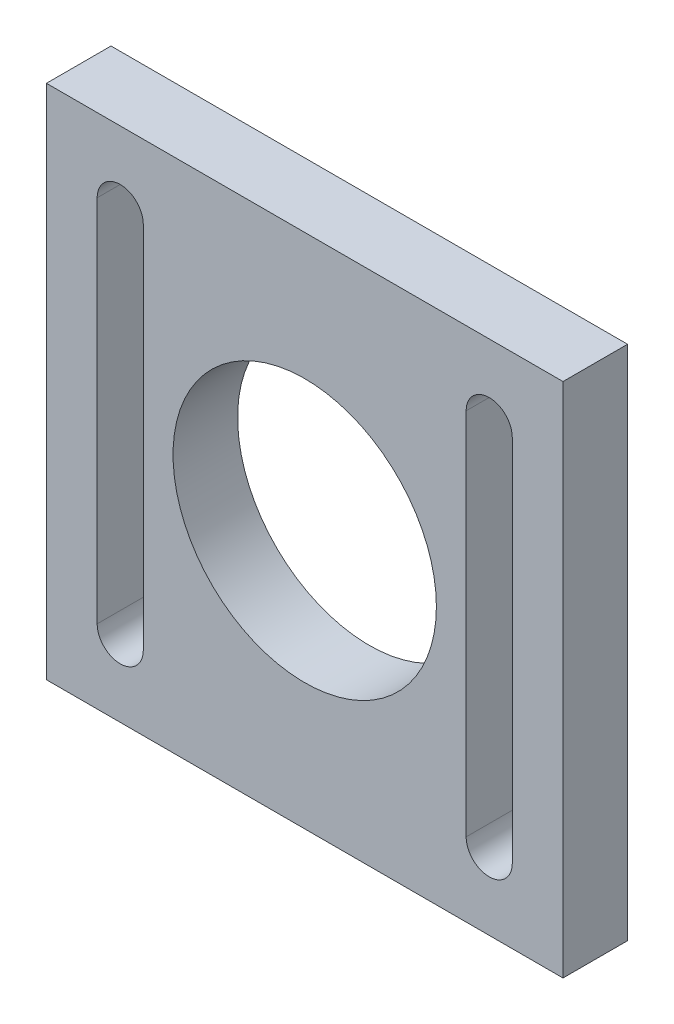
SolidWorks part; units mm, degrees
ref_plane "Front Plane" through (0, 0, 0) normal (0, 0, 1) x (1, 0, 0)
ref_plane "Top Plane" through (0, 0, 0) normal (0, 1, 0) x (1, 0, 0)
ref_plane "Right Plane" through (0, 0, 0) normal (1, 0, 0) x (0, 0, -1)
sketch "Sketch1" plane through (0, 0, 0) normal (0, 0, 1) x (1, 0, 0)
  line L1 (0, 0) -> (56, 0)
  line L2 (0, 0) -> (0, 56)
  line L3 (0, 56) -> (56, 56)
  line L4 (56, 0) -> (56, 56)
  dimension "D1" = 56
  dimension "D2" = 56
extrude "Boss-Extrude1" add sketch "Sketch1" along normal blind 7 contours L3 L4 L1 L2
sketch "Sketch2" plane through (0, 0, 7) normal (0, 0, 1) x (1, 0, 0)
  line L0 (28, 56) -> (28, 0) construction
  line L1 (0, 56) -> (56, 56) construction
  line L2 (0, 0) -> (56, 0) construction
  line L3 (0, 28) -> (56, 28) construction
  line L4 (0, 0) -> (0, 56) construction
  line L5 (56, 0) -> (56, 56) construction
  line L6 (8, 48) -> (8, 8) construction
  line L7 (10.5, 48) -> (10.5, 8)
  line L8 (5.5, 48) -> (5.5, 8)
  line L9 (48, 48) -> (48, 8) construction
  line L10 (50.5, 48) -> (50.5, 8)
  line L11 (45.5, 48) -> (45.5, 8)
  circle A0 centre (28, 28) radius 14.275
  arc A5 (10.5, 48) -> (5.5, 48) centre (8, 48) ccw
  arc A6 (5.5, 8) -> (10.5, 8) centre (8, 8) ccw
  arc A7 (50.5, 48) -> (45.5, 48) centre (48, 48) ccw
  arc A8 (45.5, 8) -> (50.5, 8) centre (48, 8) ccw
  point P22 (8, 28)
  point P27 (48, 28)
  dimension "D1" = 28.55
  dimension "D6" = 8
  dimension "D7" = 8
  dimension "D8" = 8
  dimension "D9" = 8
  dimension "D10" = 8
  dimension "D11" = 8
  dimension "D12" = 8
  dimension "D13" = 8
  dimension "D14" = 5
  dimension "D15" = 5
extrude "Cut-Extrude1" cut sketch "Sketch2" against normal through all
